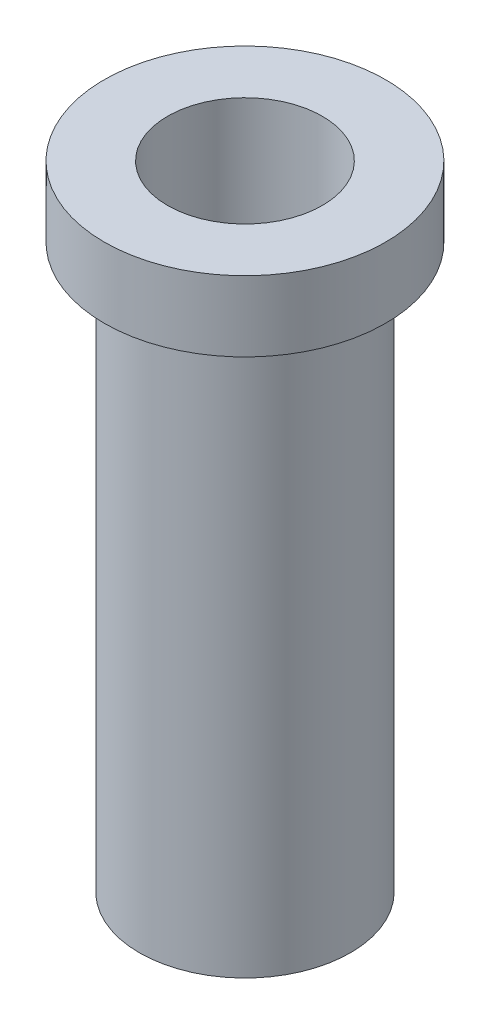
SolidWorks part; units mm, degrees
ref_plane "Front Plane" through (0, 0, 0) normal (0, 0, 1) x (1, 0, 0)
ref_plane "Top Plane" through (0, 0, 0) normal (0, 1, 0) x (1, 0, 0)
ref_plane "Right Plane" through (0, 0, 0) normal (1, 0, 0) x (0, 0, -1)
sketch "Sketch1" plane through (0, 0, 0) normal (0, 1, 0) x (1, 0, 0)
  circle A0 centre (0, 0) radius 7.5
  dimension "D1" = 15
extrude "Boss-Extrude1" add sketch "Sketch1" along normal blind 40
sketch "Sketch2" plane through (0, 40, 0) normal (0, 1, 0) x (1, 0, 0)
  circle A0 centre (0, 0) radius 10
  dimension "D1" = 20
extrude "Boss-Extrude2" add sketch "Sketch2" along normal blind 5
sketch "Sketch3" plane through (0, 45, 0) normal (0, 1, 0) x (1, 0, 0)
  circle A0 centre (0, 0) radius 5.5
  dimension "D1" = 11
extrude "Cut-Extrude1" cut sketch "Sketch3" against normal up to next
